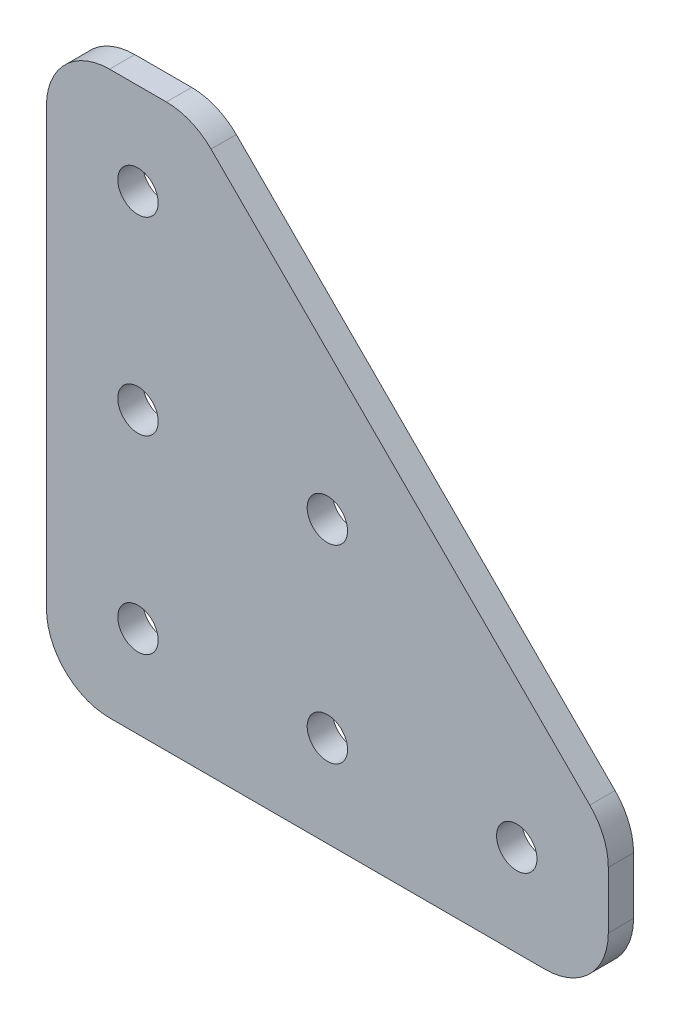
SolidWorks part; units mm, degrees
ref_plane "Front Plane" through (0, 0, 0) normal (0, 0, 1) x (1, 0, 0)
ref_plane "Top Plane" through (0, 0, 0) normal (0, 1, 0) x (1, 0, 0)
ref_plane "Right Plane" through (0, 0, 0) normal (1, 0, 0) x (0, 0, -1)
sketch "Sketch1" plane through (0, 0, 0) normal (0, 0, 1) x (1, 0, 0)
  line L0 (13.0355, 43.0355) -> (43.0355, 13.0355)
  line L1 (5, 0) -> (39.5, 0)
  line L2 (0, 5) -> (0, 39.5)
  line L3 (5, 44.5) -> (9.5, 44.5)
  line L4 (44.5, 5) -> (44.5, 9.5)
  line L5 (-8.4223, 7.25) -> (53.6618, 7.25) construction
  line L6 (7.25, -7.2744) -> (7.25, 55.1733) construction
  line L7 (5, 14.5) -> (39.5, 14.5) construction
  line L8 (7.25, 37.25) -> (37.25, 7.25) construction
  arc A0 (0, 39.5) -> (5, 44.5) centre (5, 39.5) cw
  arc A1 (13.0355, 43.0355) -> (9.5, 44.5) centre (9.5, 39.5) ccw
  arc A2 (43.0355, 13.0355) -> (44.5, 9.5) centre (39.5, 9.5) cw
  arc A3 (39.5, 0) -> (44.5, 5) centre (39.5, 5) ccw
  arc A4 (0, 5) -> (5, 0) centre (5, 5) ccw
  circle A5 centre (7.25, 7.25) radius 1.6
  circle A6 centre (7.25, 22.25) radius 1.6
  circle A7 centre (7.25, 37.25) radius 1.6
  circle A8 centre (22.25, 7.25) radius 1.6
  circle A9 centre (37.25, 7.25) radius 1.6
  circle A10 centre (22.25, 22.25) radius 1.6
  point P16 (0, 0)
  dimension "D1" = 5
  dimension "D4" = 3.2
  dimension "D2" = 44.5
  dimension "D3" = 44.5
  dimension "D5" = 7.25
  dimension "D6" = 7.25
  dimension "D7" = 15
  dimension "D8" = 15
  dimension "D9" = 15
  dimension "D10" = 15
extrude "Boss-Extrude1" add sketch "Sketch1" along normal blind 2
